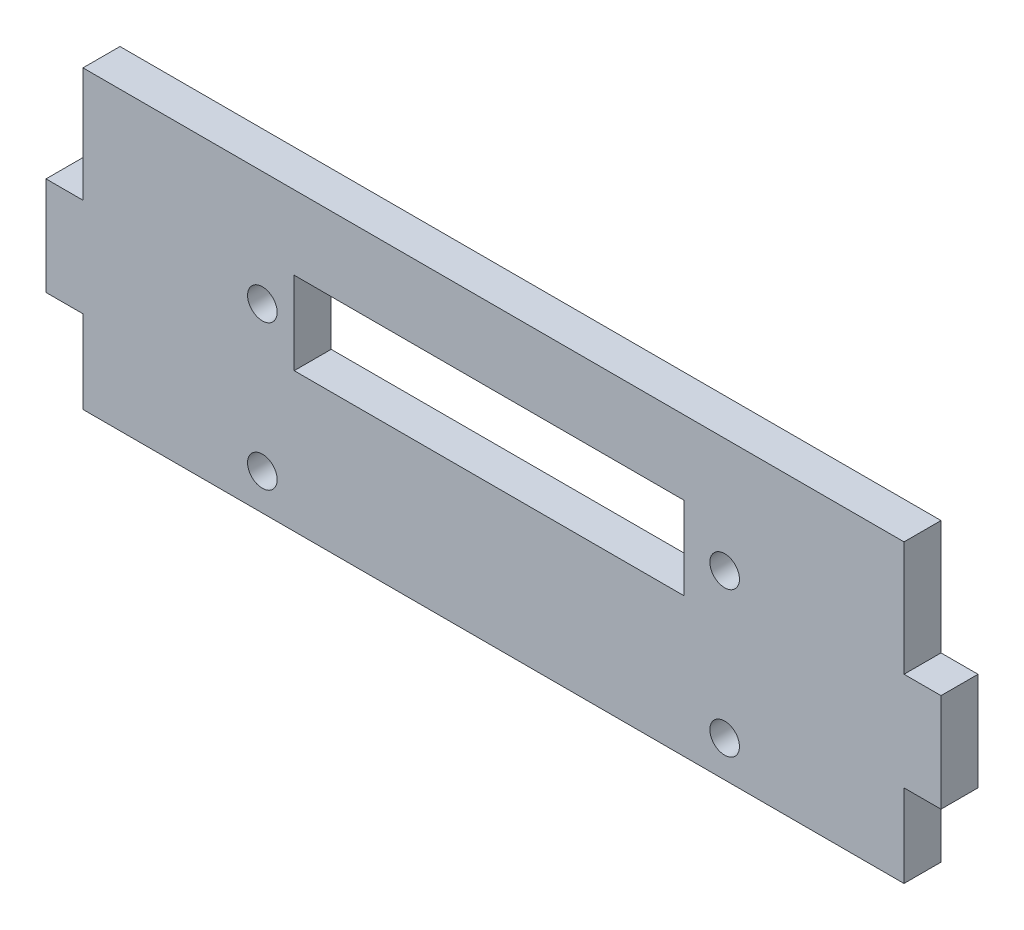
SolidWorks part; units mm, degrees
ref_plane "Alzado" through (0, 0, 0) normal (0, 0, 1) x (1, 0, 0)
ref_plane "Planta" through (0, 0, 0) normal (0, 1, 0) x (1, 0, 0)
ref_plane "Vista lateral" through (0, 0, 0) normal (1, 0, 0) x (0, 0, -1)
sketch "Croquis1" plane through (0, 0, 0) normal (0, 0, 1) x (1, 0, 0)
  line L1 (0, 0) -> (111, 0)
  line L2 (0, 0) -> (0, 40)
  line L3 (0, 40) -> (111, 40)
  line L4 (111, 0) -> (111, 40)
  dimension "D1" = 40
  dimension "D2" = 111
extrude "Saliente-Extruir1" add sketch "Croquis1" along normal blind 5
sketch "Croquis2" plane through (0, 0, 5) normal (0, 0, 1) x (1, 0, 0)
  line L0 (0, 24.5) -> (111, 24.5) construction
  line L1 (0, 40) -> (0, 0) construction
  line L2 (111, 0) -> (111, 40) construction
  line L3 (111, 40) -> (0, 40) construction
  line L4 (0, 4.9) -> (111, 4.9) construction
  line L5 (0, 0) -> (111, 0) construction
  line L7 (28.5555, 30) -> (81.2555, 30)
  line L8 (28.5555, 30) -> (28.5555, 18.8204)
  line L9 (28.5555, 18.8204) -> (81.2555, 18.8204)
  line L10 (81.2555, 30) -> (81.2555, 18.8204)
  circle A0 centre (24.25, 24.5) radius 2
  circle A1 centre (86.75, 24.5) radius 2
  circle A2 centre (24.25, 4.9) radius 2
  circle A3 centre (86.75, 4.9) radius 2
  point P12 (55.5, 24.5)
  dimension "D1" = 4
  dimension "D2" = 4
  dimension "D7" = 4
  dimension "D8" = 31.25
  dimension "D3" = 15.5
  dimension "D4" = 31.25
  dimension "D5" = 31.25
  dimension "D6" = 4.9
  dimension "D9" = 31.25
  dimension "D10" = 10
  dimension "D11" = 52.7
extrude "Cortar-Extruir1" cut sketch "Croquis2" against normal blind 10
sketch "Croquis3" plane through (0, 0, 0) normal (-1, 0, 0) x (0, 0, 1)
  line L0 (0, 40) -> (0, 0) construction
  line L1 (0, 24.5) -> (5, 24.5)
  line L2 (0, 24.5) -> (0, 11.2)
  line L3 (0, 11.2) -> (5, 11.2)
  line L4 (5, 24.5) -> (5, 11.2)
  line L5 (5, 40) -> (5, 0) construction
  line L6 (5, 40) -> (0, 40) construction
  dimension "D1" = 13.3
  dimension "D2" = 15.5
extrude "Saliente-Extruir2" add sketch "Croquis3" along normal blind 5
sketch "Croquis4" plane through (111, 0, 0) normal (1, 0, 0) x (0, 0, -1)
  line L1 (-5, 24.5) -> (0, 24.5)
  line L2 (-5, 24.5) -> (-5, 11.2)
  line L3 (-5, 11.2) -> (0, 11.2)
  line L4 (0, 24.5) -> (0, 11.2)
extrude "Saliente-Extruir3" add sketch "Croquis4" along normal blind 5
sketch "Croquis5" plane through (0, 0, 5) normal (0, 0, 1) x (1, 0, 0)
  line L0 (28.5555, 30) -> (28.5555, 18.8204) construction
  line L1 (81.2555, 30) -> (28.5555, 30) construction
  line L2 (81.2555, 18.8204) -> (81.2555, 30) construction
  line L3 (28.5555, 18.8204) -> (81.2555, 18.8204) construction
  line L4 (28.5555, 30) -> (28.5555, 18.8204)
  line L5 (81.2555, 30) -> (28.5555, 30)
  line L6 (81.2555, 18.8204) -> (81.2555, 30)
  line L7 (28.5555, 18.8204) -> (81.2555, 18.8204)
  line L12 (0, 40) -> (0, 24.5)
  line L13 (0, 24.5) -> (-5, 24.5)
  line L14 (-5, 24.5) -> (-5, 11.2)
  line L15 (-5, 11.2) -> (0, 11.2)
  line L16 (0, 11.2) -> (0, 0)
  line L17 (0, 0) -> (111, 0)
  line L18 (111, 0) -> (111, 11.2)
  line L19 (111, 11.2) -> (116, 11.2)
  line L20 (116, 11.2) -> (116, 24.5)
  line L21 (116, 24.5) -> (111, 24.5)
  line L22 (111, 24.5) -> (111, 40)
  line L23 (111, 40) -> (0, 40)
  line L24 (0, 40) -> (0, 24.5)
  line L25 (0, 24.5) -> (-5, 24.5)
  line L26 (-5, 24.5) -> (-5, 11.2)
  line L27 (-5, 11.2) -> (0, 11.2)
  line L28 (0, 11.2) -> (0, 0)
  line L29 (0, 0) -> (111, 0)
  line L30 (111, 0) -> (111, 11.2)
  line L31 (111, 11.2) -> (116, 11.2)
  line L32 (116, 11.2) -> (116, 24.5)
  line L33 (116, 24.5) -> (111, 24.5)
  line L34 (111, 24.5) -> (111, 40)
  line L35 (111, 40) -> (0, 40)
  circle A0 centre (86.75, 24.5) radius 2 construction
  circle A1 centre (86.75, 4.9) radius 2 construction
  circle A2 centre (24.25, 4.9) radius 2 construction
  circle A3 centre (24.25, 24.5) radius 2 construction
  circle A4 centre (86.75, 24.5) radius 2
  circle A5 centre (86.75, 4.9) radius 2
  circle A6 centre (24.25, 4.9) radius 2
  circle A7 centre (24.25, 24.5) radius 2
  dimension "D1" = 0
